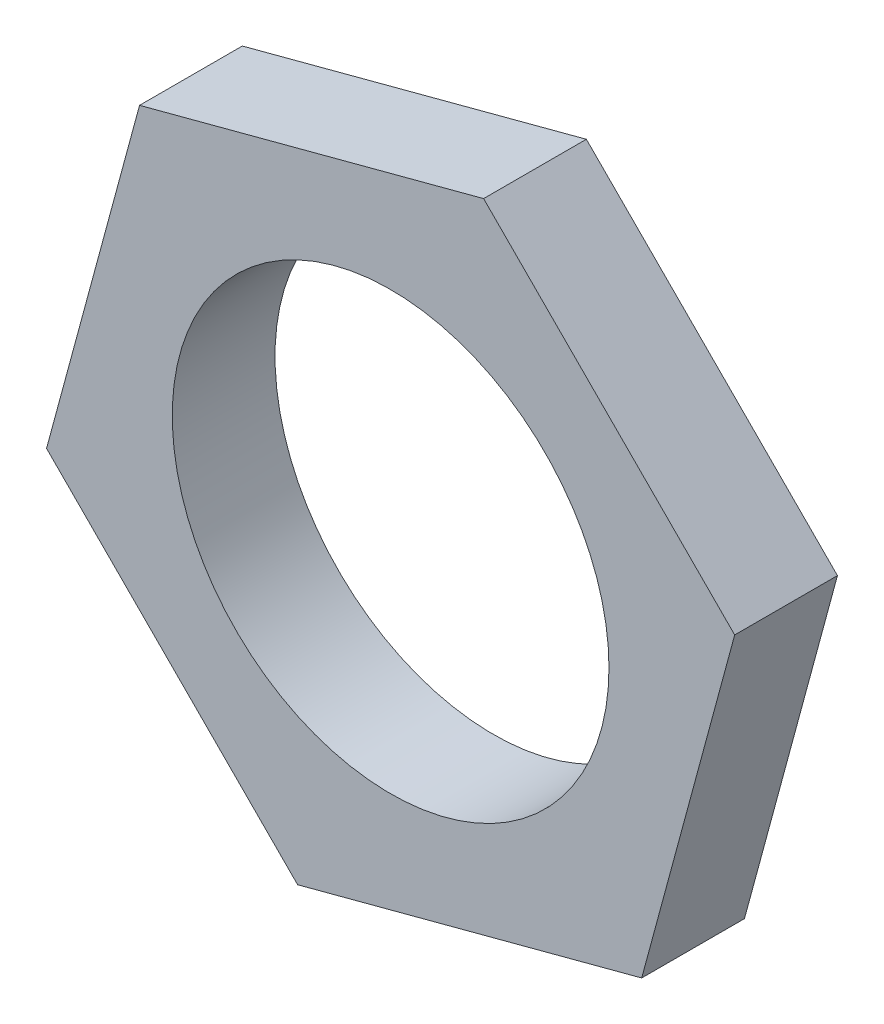
SolidWorks part; units mm, degrees
ref_plane "Front Plane" through (0, 0, 0) normal (0, 0, 1) x (1, 0, 0)
ref_plane "Top Plane" through (0, 0, 0) normal (0, 1, 0) x (1, 0, 0)
ref_plane "Right Plane" through (0, 0, 0) normal (1, 0, 0) x (0, 0, -1)
sketch "Sketch1" plane through (0, 0, 0) normal (0, 0, 1) x (1, 0, 0)
  line L1 (4.8867, -4.9112) -> (6.6966, 1.7764)
  line L2 (6.6966, 1.7764) -> (1.8099, 6.6876)
  line L3 (1.8099, 6.6876) -> (-4.8867, 4.9112)
  line L4 (-4.8867, 4.9112) -> (-6.6966, -1.7764)
  line L5 (-6.6966, -1.7764) -> (-1.8099, -6.6876)
  line L6 (-1.8099, -6.6876) -> (4.8867, -4.9112)
  circle A0 centre (0, 0) radius 6 construction
  circle A1 centre (0, 0) radius 4.25
  dimension "D2" = 8.5
  dimension "D1" = 12
extrude "Boss-Extrude1" add sketch "Sketch1" along normal blind 2
